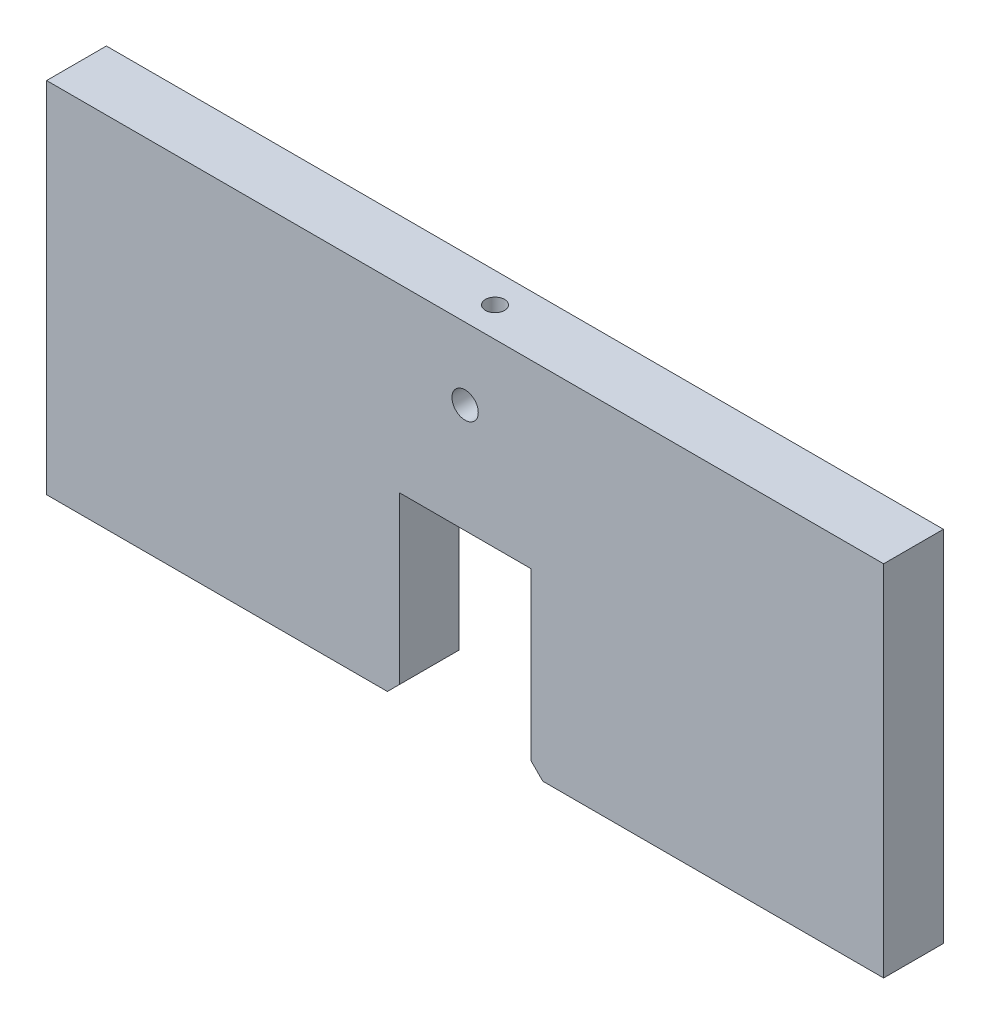
SolidWorks part; units mm, degrees
material "Plain Carbon Steel"
ref_plane "Front Plane" through (0, 0, 0) normal (0, 0, 1) x (1, 0, 0)
ref_plane "Top Plane" through (0, 0, 0) normal (0, 1, 0) x (1, 0, 0)
ref_plane "Right Plane" through (0, 0, 0) normal (1, 0, 0) x (0, 0, -1)
sketch "Sketch1" plane through (0, 0, 0) normal (0, 0, 1) x (1, 0, 0)
  line B0 (350, 232.4214) -> (-350, 232.4214)
  line B1 (-350, 232.4214) -> (-350, -67.5786)
  line B2 (-350, -67.5786) -> (-65, -67.5786)
  line B3 (-65, -67.5786) -> (-55, -57.5786)
  line B4 (-55, 81.4214) -> (55, 81.4214)
  line B5 (-55, -57.5786) -> (-55, 81.4214)
  line B6 (55, -57.5786) -> (55, 81.4214)
  line B7 (65, -67.5786) -> (55, -57.5786)
  line B8 (350, -67.5786) -> (65, -67.5786)
  line B9 (350, 232.4214) -> (350, -67.5786)
sketch_block_instance "Ballast_block-1"
sketch_block "Ballast_block" parameters "D1"=135, "D2"=10, "D3"=230, "D4"=230, "D5"=299, "D6"=285
extrude "Boss-Extrude1" add sketch "Sketch1" along normal mid plane 50
sketch "Sketch2" plane through (0, 0, 0) normal (0, 0, 1) x (1, 0, 0)
  line L0 (0, 0) -> (0, 241.1048) construction
  line L1 (350, 232.4214) -> (-350, 232.4214) construction
  circle A0 centre (0, 172.4214) radius 11
  dimension "D1" = 22
  dimension "D2" = 60
extrude "Cut-Extrude1" cut sketch "Sketch2" against normal through all and the other way through all
sketch "Sketch3" plane through (0, 232.4214, 0) normal (0, 1, 0) x (1, 0, 0)
  circle A0 centre (0, 0) radius 8
  dimension "D1" = 16
extrude "Cut-Extrude2" cut sketch "Sketch3" against normal blind 35
sketch "Sketch4" plane through (0, -67.5786, 0) normal (0, -1, 0) x (1, 0, 0)
  line L0 (-350, 0) -> (350, 0) construction
  line L1 (-350, 25) -> (-350, -25) construction
  line L2 (350, 25) -> (350, -25) construction
  circle A0 centre (-80, 0) radius 8
  circle A1 centre (80, 0) radius 8
  dimension "D3" = 16
  dimension "D4" = 16
  dimension "D1" = 80
  dimension "D2" = 80
extrude "Cut-Extrude3" cut sketch "Sketch4" against normal blind 30
